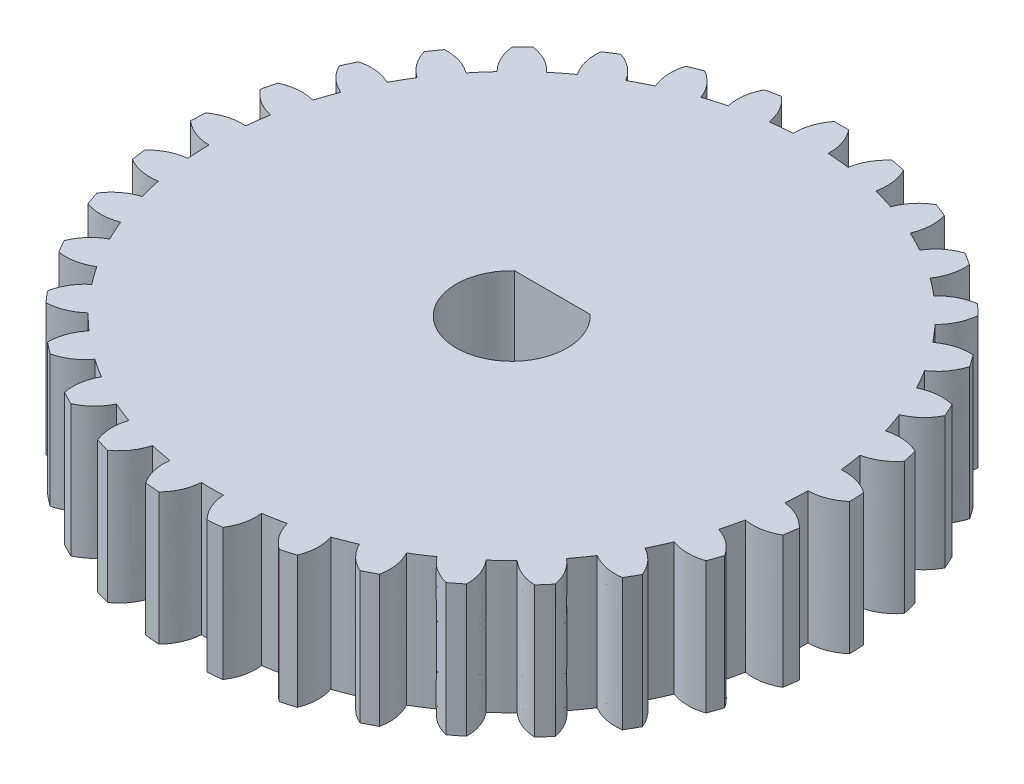
SolidWorks part; units mm, degrees
ref_plane "Front Plane" through (0, 0, 0) normal (0, 0, 1) x (1, 0, 0)
ref_plane "Top Plane" through (0, 0, 0) normal (0, 1, 0) x (1, 0, 0)
ref_plane "Right Plane" through (0, 0, 0) normal (1, 0, 0) x (0, 0, -1)
sketch "Sketch1" plane through (0, 0, 0) normal (0, 1, 0) x (1, 0, 0)
  line L0 (0, 0) -> (0, 11.2297) construction
  line L1 (0, 0) -> (-0.2501, 11.2792) construction
  line L2 (0, 0) -> (-0.6395, 10.9248) construction
  line L3 (0, 0) -> (-0.977, 10.1465) construction
  line L4 (0, 0) -> (1.0447, 10.8498)
  line L5 (0, 0) -> (-1.0447, 10.8498)
  line L8 (0, 0) -> (-0.5859, 12.3332) construction
  circle A0 centre (0, 0) radius 12 construction
  circle A1 centre (0, 0) radius 10.9 construction
  circle A2 centre (0, 0) radius 11.5 construction
  arc A3 (0.266, 11.9971) -> (0, 12) centre (0, 0) ccw
  arc A4 (-0.6369, 10.8814) -> (-1.0447, 10.8498) centre (0, 0) ccw
  arc A5 (-0.266, 11.9971) -> (0, 12) centre (0, 0) cw
  arc A6 (0.6369, 10.8814) -> (1.0447, 10.8498) centre (0, 0) cw
  spline S0 degree 2 poles (-0.6369, 10.8814) (-0.6497, 11.5061) (-0.266, 11.9971) knots 0 0 0 1 1 1
  spline S1 degree 2 poles (0.6369, 10.8814) (0.6497, 11.5061) (0.266, 11.9971) knots 0 0 0 1 1 1
  point P14 (-0.841, 10.8675)
  point P19 (-0.133, 11.9993)
  dimension "D1" = 24
  dimension "D2" = 21.8
  dimension "D3" = 23
  dimension "D7" = 2.72
  dimension "D4" = 1.27
  dimension "D5" = 3.35
  dimension "D6" = 5.5
extrude "Boss-Extrude1" add sketch "Sketch1" along normal blind 4.8
ref_axis "Axis1" through (0, 3.675, 0) along (0, -1, 0)
pattern_circular "CirPattern1" count 33 over 360 about axis through (0, 3.675, 0) along (0, -1, 0) of "Boss-Extrude1"
sketch "Sketch7" plane through (0, 0, 0) normal (0, -1, 0) x (1, 0, 0)
  circle A0 centre (0, 0) radius 4.7
  dimension "D1" = 9.4
sketch "Sketch8" plane through (0, 4.8, 0) normal (0, 1, 0) x (1, 0, 0)
  circle A0 centre (0, 0) radius 4.7
  dimension "D1" = 9.4
sketch "Sketch9" plane through (0, 4.8, 0) normal (0, 1, 0) x (1, 0, 0)
  line L0 (0, 1.6202) -> (0, -1.6327) construction
  line L1 (-1.375, 1.4798) -> (1.375, 1.4798)
  line L2 (-1.5614, 0) -> (1.8463, 0) construction
  circle A0 centre (0, 0) radius 2.02 construction
  arc A1 (-1.375, 1.4798) -> (1.375, 1.4798) centre (0, 0) ccw
  point P4 (0, 1.4798)
  dimension "D1" = 4.04
  dimension "D2" = 2.75
extrude "Cut-Extrude1" cut sketch "Sketch9" against normal up to surface (4.8 mm away) up to face at (0, 0, 0)
